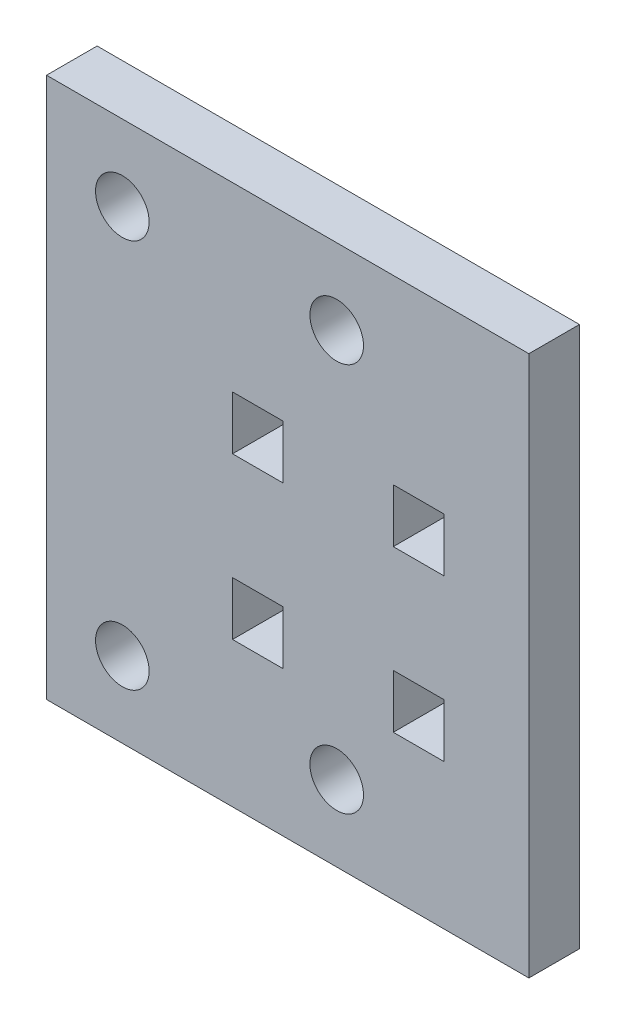
SolidWorks part; units mm, degrees
ref_plane "Front Plane" through (0, 0, 0) normal (0, 0, 1) x (1, 0, 0)
ref_plane "Top Plane" through (0, 0, 0) normal (0, 1, 0) x (1, 0, 0)
ref_plane "Right Plane" through (0, 0, 0) normal (1, 0, 0) x (0, 0, -1)
sketch "Sketch1" plane through (0, 0, 0) normal (0, 0, 1) x (-1, 0, 0)
  line L0 (34.0796, -5.532) -> (40.074, -5.532)
  line L1 (15.0296, 13.518) -> (21.024, 13.518)
  line L2 (15.0296, 13.518) -> (15.0296, 7.3689)
  line L3 (15.0296, 7.168) -> (21.024, 7.168)
  line L4 (21.024, 13.518) -> (21.024, 7.3689)
  line L5 (21.024, -11.882) -> (21.024, -5.532)
  line L6 (15.0296, -5.532) -> (15.0296, -11.882)
  line L7 (15.0296, -11.882) -> (21.024, -11.882)
  line L8 (62.1098, 30.6992) -> (62.1098, -33.3613)
  line L9 (62.1098, -33.3613) -> (4.9598, -33.3613)
  line L10 (4.9598, -33.3613) -> (4.9598, 30.6992)
  line L11 (4.9598, 30.6992) -> (62.1098, 30.6992)
  line L13 (40.074, 7.3689) -> (40.074, 7.168)
  line L14 (34.0796, 7.3689) -> (34.0796, 7.168)
  line L15 (40.074, -11.882) -> (34.0796, -11.882)
  line L16 (40.074, -5.532) -> (40.074, -11.882)
  line L18 (34.0796, -11.882) -> (34.0796, -5.532)
  line L19 (34.0796, 13.518) -> (34.0796, 7.3689)
  line L20 (40.074, 7.168) -> (34.0796, 7.168)
  line L21 (40.074, 13.518) -> (40.074, 7.3689)
  line L22 (40.074, 13.518) -> (34.0796, 13.518)
  line L27 (21.024, 7.3689) -> (21.024, 7.168)
  line L28 (15.0296, 7.3689) -> (15.0296, 7.168)
  line L29 (21.024, -5.532) -> (15.0296, -5.532)
  circle A0 centre (53.1296, -24.3811) radius 3.175
  circle A1 centre (53.1296, 21.7189) radius 3.175
  circle A2 centre (27.7296, -24.3811) radius 3.175
  circle A3 centre (27.7296, 21.7189) radius 3.175
extrude "Boss-Extrude1" add sketch "Sketch1" along normal blind 5.9944 contours L8 L9 L10 L11
